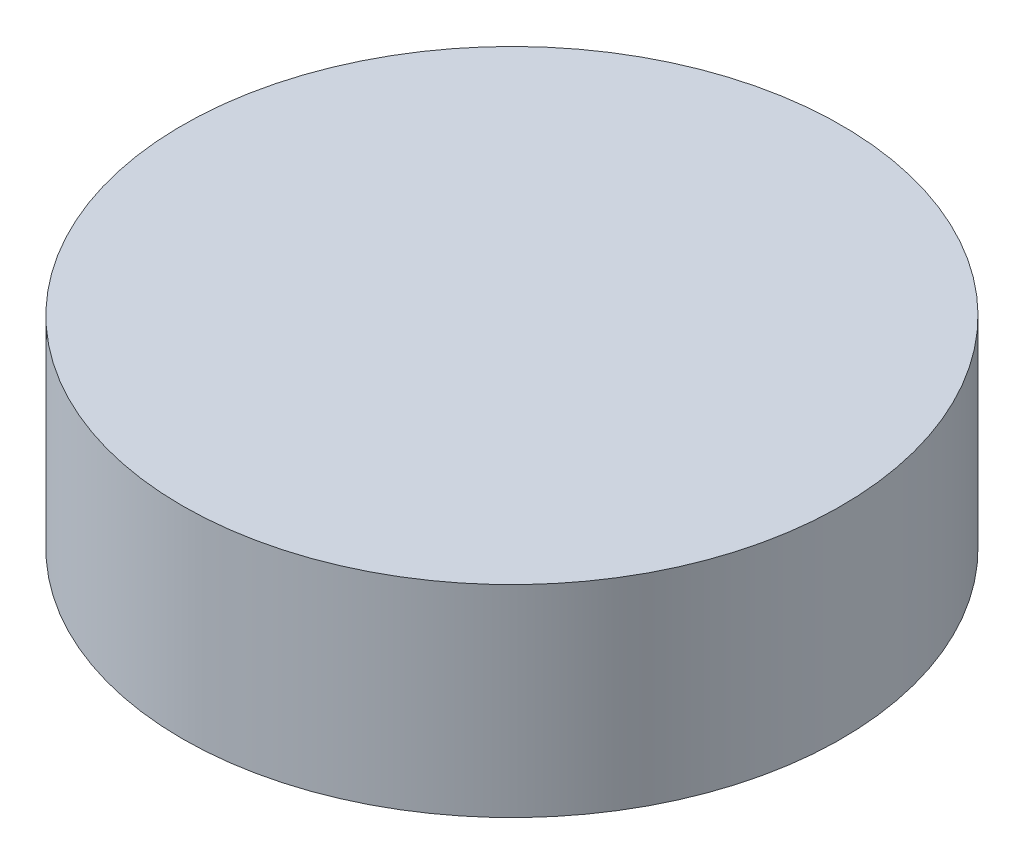
SolidWorks part; units mm, degrees
ref_plane "Front Plane" through (0, 0, 0) normal (0, 0, 1) x (1, 0, 0)
ref_plane "Top Plane" through (0, 0, 0) normal (0, 1, 0) x (1, 0, 0)
ref_plane "Right Plane" through (0, 0, 0) normal (1, 0, 0) x (0, 0, -1)
sketch "Sketch1" plane through (0, 0, 0) normal (0, 1, 0) x (1, 0, 0)
  circle A0 centre (0, 0) radius 49
  dimension "D1" = 98
extrude "Boss-Extrude1" add sketch "Sketch1" along normal blind 30
